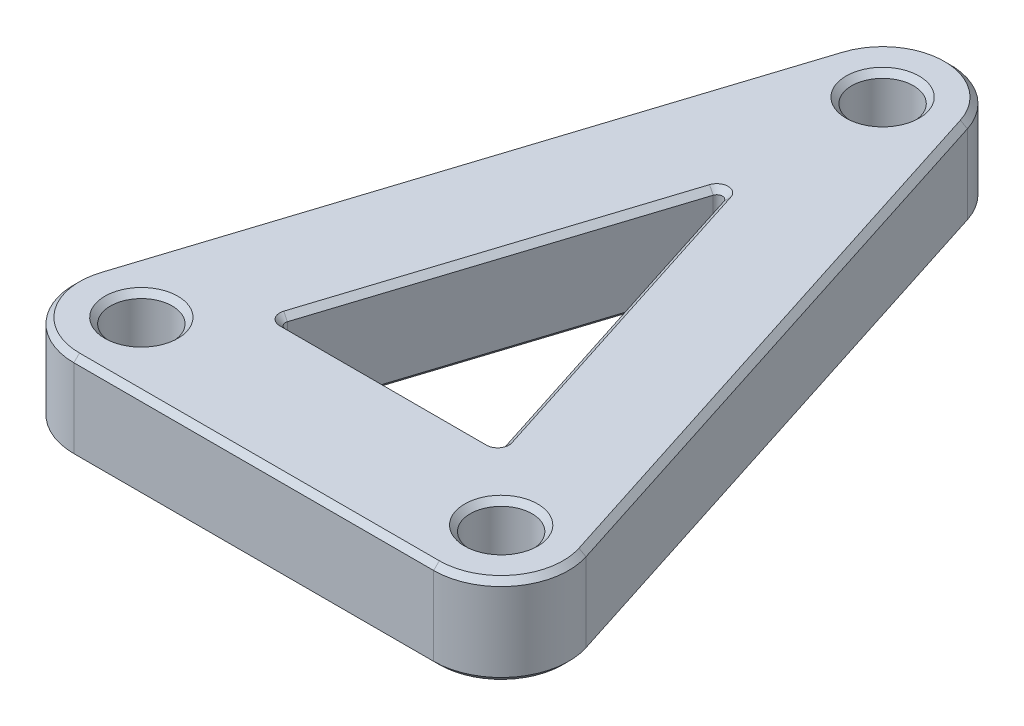
SolidWorks part; units mm, degrees
ref_plane "Front Plane" through (0, 0, 0) normal (0, 0, 1) x (1, 0, 0)
ref_plane "Top Plane" through (0, 0, 0) normal (0, 1, 0) x (1, 0, 0)
ref_plane "Right Plane" through (0, 0, 0) normal (1, 0, 0) x (0, 0, -1)
sketch "Sketch1" plane through (0, 0, 0) normal (0, 1, 0) x (1, 0, 0)
  line L0 (-4.5352, 1.4536) -> (-17.2352, -38.1704)
  line L1 (4.5352, 1.4536) -> (17.2352, -38.1704)
  line L2 (-12.7, -44.3865) -> (12.7, -44.3865)
  line L3 (-0.3779, -11.5815) -> (-7.6734, -34.3435)
  line L4 (-7.2955, -34.8615) -> (7.2955, -34.8615)
  line L5 (7.6734, -34.3435) -> (0.3779, -11.5815)
  circle A0 centre (0, 0) radius 2.1828
  circle A1 centre (12.7, -39.624) radius 2.1828
  circle A2 centre (-12.7, -39.624) radius 2.1828
  arc A3 (4.5352, 1.4536) -> (-4.5352, 1.4536) centre (0, 0) ccw
  arc A4 (12.7, -44.3865) -> (17.2352, -38.1704) centre (12.7, -39.624) ccw
  arc A5 (-17.2352, -38.1704) -> (-12.7, -44.3865) centre (-12.7, -39.624) ccw
  arc A6 (7.2955, -34.8615) -> (7.6734, -34.3435) centre (7.2955, -34.4646) ccw
  arc A7 (-7.6734, -34.3435) -> (-7.2955, -34.8615) centre (-7.2955, -34.4646) ccw
  arc A8 (-0.3779, -11.5815) -> (0.3779, -11.5815) centre (0, -11.7027) cw
  dimension "D4" = 4.3656
  dimension "D5" = 4.3656
  dimension "D6" = 4.3656
  dimension "D7" = 9.525
  dimension "D8" = 9.525
  dimension "D9" = 9.525
  dimension "D13" = 0.3969
  dimension "D1" = 39.624
  dimension "D2" = 12.7
  dimension "D3" = 12.7
  dimension "D10" = 9.525
  dimension "D11" = 7.9375
  dimension "D12" = 7.9375
extrude "Boss-Extrude2" add sketch "Sketch1" along normal blind 6.35
chamfer "Chamfer2" distance 0.3969 angle 45 30 edges at (0, 0, 34.8615) (-7.6161, 0, 34.6985) (-4.0257, 0, 22.9625) (0, 0, 11.3058) (4.0257, 0, 22.9625) (7.6161, 0, 34.6985) (-10.8852, 0, 18.3584) (-16.5473, 0, 42.431) (0, 0, 44.3865) (16.5473, 0, 42.431) (10.8852, 0, 18.3584) (0, 0, -4.7625) (0, 0, 2.1828) (12.7, 0, 41.8068) (-12.7, 0, 41.8068) (0, 6.35, 11.3058) (-4.0257, 6.35, 22.9625) (-7.6161, 6.35, 34.6985) (0, 6.35, 34.8615) (7.6161, 6.35, 34.6985) (4.0257, 6.35, 22.9625) (-12.7, 6.35, 41.8068) (0, 6.35, 2.1828) (10.8852, 6.35, 18.3584) (16.5473, 6.35, 42.431) (0, 6.35, 44.3865) (-16.5473, 6.35, 42.431) (-10.8852, 6.35, 18.3584) (0, 6.35, -4.7625) (12.7, 6.35, 41.8068)
